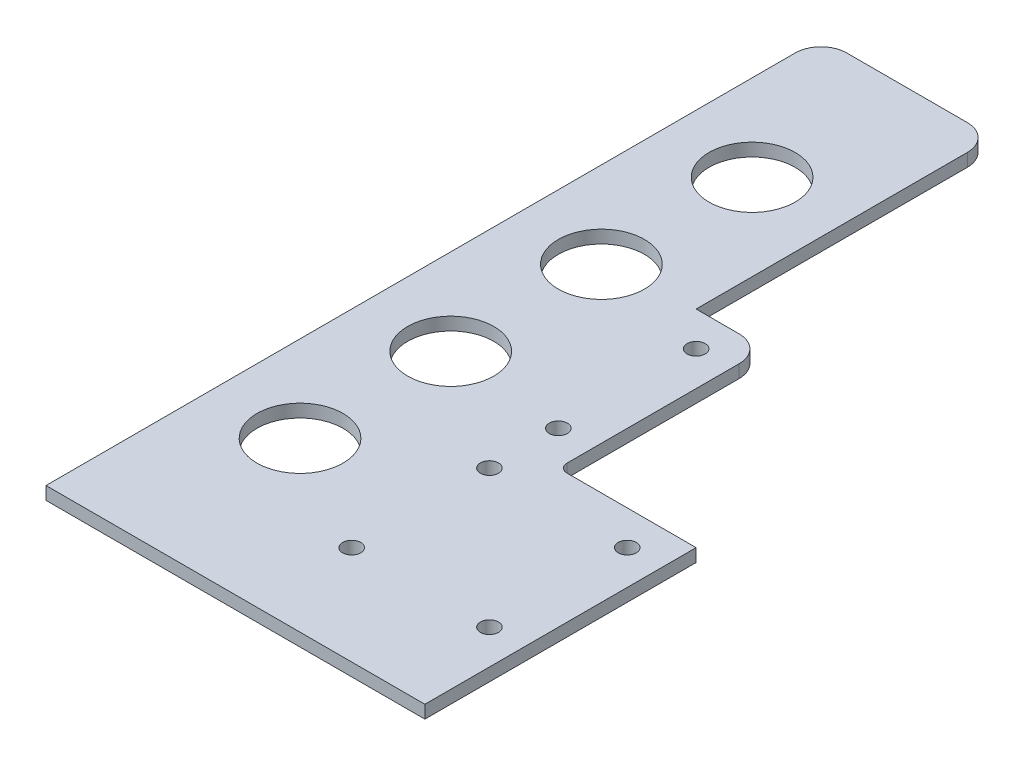
SolidWorks part; units mm, degrees
ref_plane "Front Plane" through (0, 0, 0) normal (0, 0, 1) x (1, 0, 0)
ref_plane "Top Plane" through (0, 0, 0) normal (0, 1, 0) x (1, 0, 0)
ref_plane "Right Plane" through (0, 0, 0) normal (1, 0, 0) x (0, 0, -1)
sketch "Sketch1" plane through (0, 0, 0) normal (0, 1, 0) x (1, 0, 0)
  line L0 (-8, 26) -> (-8, 66)
  line L7 (-16, -16) -> (16, -16) construction
  line L8 (-16, -16) -> (-16, 16) construction
  line L9 (-16, 16) -> (16, 16) construction
  line L10 (16, -16) -> (16, 16) construction
  line L11 (-16, -16) -> (16, 16) construction
  line L12 (-16, 16) -> (16, -16) construction
  line L13 (-24, -43) -> (24, -43)
  line L14 (24, 24) -> (24, -43)
  line L15 (-14, 72) -> (-24, 72)
  line L17 (-6, 24) -> (24, 24)
  line L18 (-24, -43) -> (-64, -43)
  line L19 (-64, -43) -> (-64, 135)
  line L20 (-58, 141) -> (-30, 141)
  line L21 (-24, 135) -> (-24, 72)
  circle A0 centre (16, 16) radius 2.1
  circle A1 centre (16, -16) radius 2.1
  circle A2 centre (-16, -16) radius 2.1
  circle A3 centre (-16, 16) radius 2.1
  circle A4 centre (-16, 24) radius 2.1 construction
  circle A5 centre (-16, 32) radius 2.1
  circle A6 centre (-16, 40) radius 2.1 construction
  circle A7 centre (-16, 48) radius 2.1 construction
  circle A8 centre (-16, 56) radius 2.1 construction
  circle A9 centre (-16, 64) radius 2.1
  arc A10 (-8, 26) -> (-6, 24) centre (-6, 26) ccw
  arc A11 (-8, 66) -> (-14, 72) centre (-14, 66) ccw
  circle A12 centre (-44, 0) radius 10
  circle A13 centre (-44, 35) radius 10
  circle A14 centre (-44, 70) radius 10
  circle A15 centre (-44, 105) radius 10
  arc A17 (-24, 135) -> (-30, 141) centre (-30, 135) ccw
  arc A18 (-64, 135) -> (-58, 141) centre (-58, 135) cw
  circle A19 centre (-44, 140) radius 10 [skipped]
  point P0 (0, 0)
  point P1 (0, 0)
  point P6 (0, 0)
  dimension "D3" = 4.2
  dimension "D7" = 2
  dimension "D11" = 6
  dimension "D13" = 20
  dimension "D15" = 6
  dimension "D1" = 32
  dimension "D2" = 32
  dimension "D4" = 36
  dimension "D5" = 43
  dimension "D6" = 24
  dimension "D8" = 20
  dimension "D10" = 8
  dimension "D12" = 40
  dimension "D9" = 7
  dimension "D14" = 5
extrude "Boss-Extrude1" add sketch "Sketch1" along normal blind 3
sketch "Sketch2" plane through (0, 3, 0) normal (0, 1, 0) x (1, 0, 0)
  line L0 (24, -43) -> (24, 24) construction
  line L1 (-64, -43) -> (24, -43)
  line L2 (-64, -43) -> (-64, -39)
  line L3 (-64, -39) -> (24, -39)
  line L4 (24, -43) -> (24, -39)
  dimension "D1" = 4
extrude "Cut-Extrude1" cut sketch "Sketch2" against normal through all both and the other way through all
